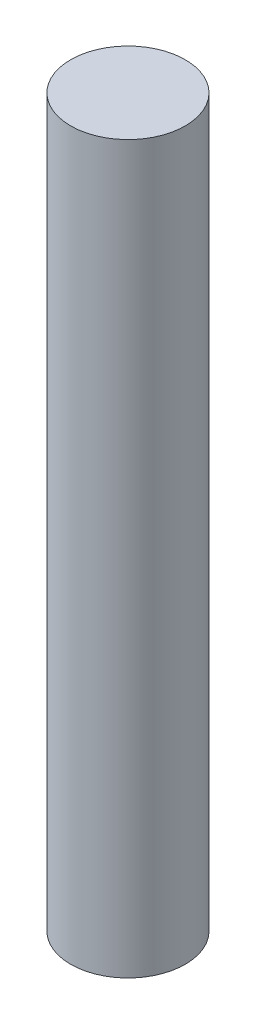
SolidWorks part; units mm, degrees
material "AISI 1045 Aço, trefilado"
ref_plane "Plano frontal" through (0, 0, 0) normal (0, 0, 1) x (1, 0, 0)
ref_plane "Plano superior" through (0, 0, 0) normal (0, 1, 0) x (1, 0, 0)
ref_plane "Plano direito" through (0, 0, 0) normal (1, 0, 0) x (0, 0, -1)
sketch "Esboço1" plane through (0, 0, 0) normal (0, 1, 0) x (1, 0, 0)
  circle A0 centre (0, 0) radius 7.5
  dimension "D1" = 15
extrude "Ressalto-extrusão1" add sketch "Esboço1" along normal blind 95
